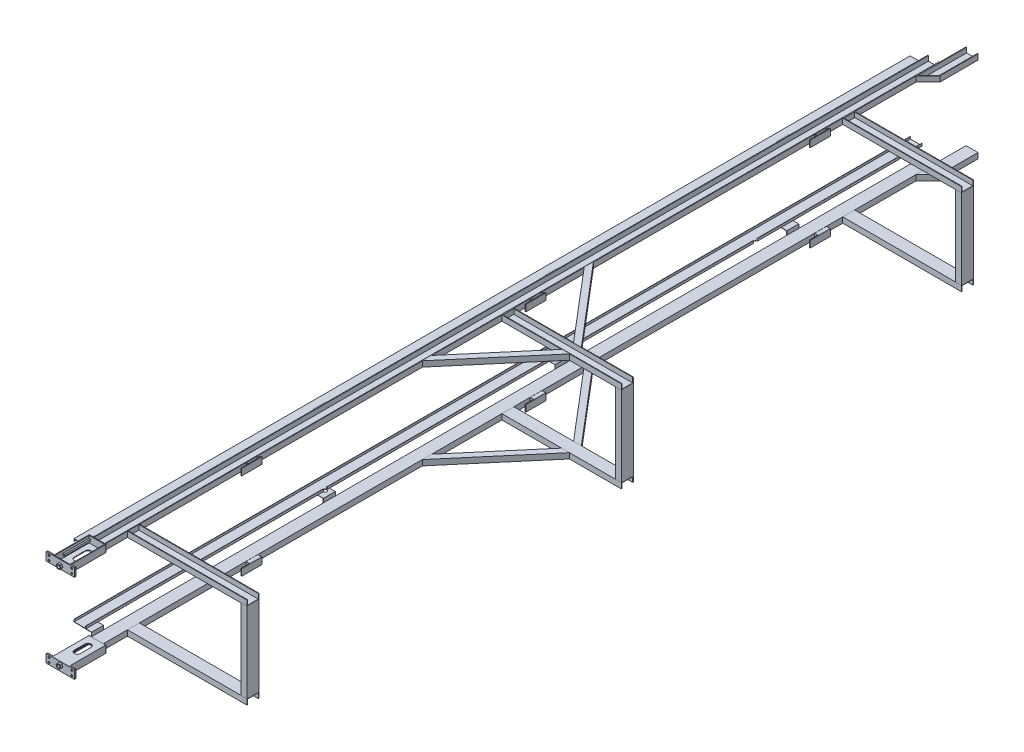
SolidWorks part; units mm, degrees
ref_plane "Front Plane" through (0, 0, 0) normal (0, 0, 1) x (1, 0, 0)
ref_plane "Top Plane" through (0, 0, 0) normal (0, 1, 0) x (1, 0, 0)
ref_plane "Right Plane" through (0, 0, 0) normal (1, 0, 0) x (0, 0, -1)
sketch "Sketch12" plane through (0, 0, 0) normal (0, 0, 1) x (1, 0, 0)
  line L0 (-50, 0) -> (50, 0)
  line L1 (-50, 0) -> (-50, 46)
  line L2 (50, 0) -> (50, 46)
  line L3 (-45, 5) -> (-45, 46)
  line L4 (-45, 5) -> (45, 5)
  line L5 (45, 5) -> (45, 46)
  line L6 (-50, 46) -> (-45, 46)
  line L7 (45, 46) -> (50, 46)
  point P2 (0, 0)
  dimension "D1" = 46
  dimension "D2" = 100
  dimension "D3" = 5
extrude "Boss-Extrude1" add sketch "Sketch12" along normal mid plane 7000
sketch "Sketch24" plane through (0, 46, 0) normal (0, 1, 0) x (1, 0, 0)
  line L0 (50, -3200) -> (1050, -3200)
  line L1 (50, -3500) -> (50, 3500) construction
  line L3 (1050, -3300) -> (50, -3300)
  line L4 (50, -3300) -> (50, -3200)
  line L5 (1050, -3300) -> (1050, -3200)
  line L6 (1050, -3200) -> (1050, 2184.4351) construction
  line L12 (45, -3500) -> (-45, -3500) construction
  line L13 (50, 2855.5299) -> (50, -3200) construction
  line L20 (50, -3200) -> (356.6139, -3200) construction
  line L21 (1050, -3200) -> (1050, -2197.7251) construction
  line L22 (50, -3200) -> (50, 1395.9752) construction
  line L23 (50, -65.672) -> (1050, -65.672)
  line L24 (50, -165.672) -> (1050, -165.672)
  line L25 (1050, -65.672) -> (1050, -165.672)
  line L26 (50, -165.672) -> (50, -65.672)
  line L27 (50, 2687.522) -> (1043.7553, 2687.522)
  line L28 (50, 2787.522) -> (1042.4967, 2787.522) construction
  line L29 (50, 2687.522) -> (50, 2787.522)
  line L30 (50, 2787.522) -> (1043.7553, 2787.522)
  line L31 (1043.7553, 2787.522) -> (1043.7553, 2687.522)
  dimension "D1" = 200
  dimension "D2" = 100
  dimension "D3" = 1000
  dimension "D6" = 100
extrude "Boss-Extrude10" add sketch "Sketch24" against normal blind 46 separate body
shell "Shell1" thickness 5
shell "Shell2" thickness 5
sketch "Sketch31" plane through (0, 46, 0) normal (0, 1, 0) x (1, 0, 0)
  line L0 (50, 2551.1384) -> (77.987, 2551.1384)
  line L1 (77.987, 2551.1384) -> (77.987, 2451.1384)
  line L2 (77.987, 2451.1384) -> (50, 2451.1384)
  line L4 (50, -3500) -> (50, 3500) construction
  line L5 (50, 2451.1384) -> (50, 2551.1384)
  dimension "D1" = 100
  dimension "D2" = 27.987
extrude "Boss-Extrude15" add sketch "Sketch31" against normal blind 45 separate body
shell "Shell4" thickness 5
sketch "Sketch33" plane through (77.987, 0, -5338.5198) normal (-1, 0, 0) x (0, 0, 1)
  line L9 (2787.3813, 1) -> (2957.3813, 1)
  line L10 (2787.3813, 1) -> (2787.3813, 56)
  line L11 (2787.3813, 56) -> (2957.3813, 56)
  line L12 (2957.3813, 1) -> (2957.3813, 56)
  dimension "D1" = 170
  dimension "D2" = 55
extrude "Boss-Extrude23" add sketch "Sketch33" against normal blind 6 separate body
pattern_linear "LPattern2" count 3 spacing 2380 along (0, 0, 1) of bodies 132 145
sketch "Sketch34" plane through (0, 0, 3500) normal (0, 0, 1) x (1, 0, 0)
  line L0 (-70, 0) -> (70, 0)
  line L1 (-50, 0) -> (50, 0) construction
  line L2 (-70, 0) -> (-70, 60)
  line L3 (0, 0) -> (0, 71.8206) construction
  line L4 (70, 0) -> (70, 60)
  line L10 (70, 60) -> (-70, 60)
  point P4 (0, 0)
  point P5 (0, 0)
  dimension "D1" = 140
  dimension "D2" = 60
extrude "Boss-Extrude25" add sketch "Sketch34" along normal blind 6 separate body
sketch "Sketch35" plane through (0, 0, 3506) normal (0, 0, 1) x (1, 0, 0)
  line L0 (70, 0) -> (70, 60) construction
  line L1 (-70, 0) -> (70, 0) construction
  line L2 (-70, 60) -> (-70, 0) construction
  line L3 (70, 0) -> (70, 60)
  line L4 (-70, 0) -> (70, 0)
  line L5 (-70, 60) -> (-70, 0)
  line L6 (-65, 60) -> (-65, 5)
  line L7 (-65, 5) -> (65, 5)
  line L8 (65, 5) -> (65, 60)
  line L9 (-70, 60) -> (-65, 60)
  line L10 (70, 60) -> (65, 60)
  dimension "D1" = 5
extrude "Boss-Extrude26" add sketch "Sketch35" along normal blind 300 separate body
sketch "Sketch36" plane through (0, 0, 3506) normal (0, 0, 1) x (1, 0, 0)
  line L0 (0, 0) -> (0, 40.4824) construction
  line L1 (-65, 5) -> (-65, 60) construction
  line L2 (-65, 39) -> (-52, 39)
  line L3 (-65, 39) -> (-65, 23)
  line L4 (-65, 23) -> (-52, 23)
  line L5 (-52, 39) -> (-52, 23)
  line L6 (52, 39) -> (52, 23)
  line L7 (65, 23) -> (52, 23)
  line L8 (65, 39) -> (65, 23)
  line L9 (65, 39) -> (52, 39)
  line L10 (65, 5) -> (-65, 5) construction
  dimension "D1" = 18
  dimension "D2" = 16
  dimension "D3" = 13
extrude "Boss-Extrude27" add sketch "Sketch36" along normal blind 220 separate body
sketch "Sketch37" plane through (0, 0, 3806) normal (0, 0, 1) x (1, 0, 0)
  line L0 (120, 0) -> (-120, 0)
  line L4 (0, 70) -> (0, 0) construction
  line L8 (-120, 70) -> (-120, 0)
  line L9 (120, 70) -> (120, 0)
  line L12 (-95.1007, 70) -> (-95.1007, 0) construction
  line L13 (-95.1007, 35) -> (-108.4029, 35) construction
  line L14 (-120, 70) -> (120, 70)
  circle A0 centre (-95.1007, 53.4578) radius 8
  circle A1 centre (-95.1007, 16.5422) radius 8
  circle A2 centre (95.1007, 16.5422) radius 8
  circle A3 centre (95.1007, 53.4578) radius 8
  point P7 (-120, 35)
  dimension "D4" = 16
  dimension "D1" = 240
  dimension "D2" = 70
extrude "Boss-Extrude28" add sketch "Sketch37" along normal blind 6 separate body
sketch "Sketch39" plane through (0, 0, 3806) normal (0, 0, -1) x (-1, 0, 0)
  line L0 (0, 0) -> (0, 26)
  circle A0 centre (0, 26) radius 13
  dimension "D2" = 26
  dimension "D1" = 26
extrude "Cut-Extrude3" cut sketch "Sketch39" against normal blind 6
sketch "Sketch43" plane through (0, 46, 0) normal (0, 1, 0) x (1, 0, 0)
  line L0 (50, 3400.0313) -> (50, 3720.0313)
  line L1 (50, -3500) -> (50, 3500) construction
  line L2 (50, 3720.0313) -> (150, 3720.0313)
  line L3 (150, 3720.0313) -> (150, 3400.0313)
  line L6 (50, 3500) -> (150, 3500) construction
  line L7 (50, 3400.0313) -> (150, 3400.0313) construction
  line L8 (150, 3400.0313) -> (50, 3300.0313)
  line L9 (50, 3400.0313) -> (50, 3300.0313)
  line L10 (45, 3500) -> (-45, 3500) construction
  dimension "D1" = 100
  dimension "D2" = 420
  dimension "D3" = 199.9687
  dimension "D4" = 100
extrude "Boss-Extrude31" add sketch "Sketch43" against normal blind 46 separate body
shell "Shell6" thickness 5
ref_plane "Plane1" through (0, -335, 0) normal (0, -1, 0) x (-1, 0, 0)
sketch "Sketch41" plane through (0, 5, 0) normal (0, 1, 0) x (1, 0, 0)
  line L0 (0, -3506) -> (0, -3249.3372) construction
  line L1 (65, -3506) -> (-65, -3506) construction
  line L2 (0, -3580) -> (0, -3670) construction
  line L3 (25, -3580) -> (25, -3670)
  line L4 (-25, -3580) -> (-25, -3670)
  line L5 (70, -3500) -> (-70, -3500) construction
  arc A0 (25, -3580) -> (-25, -3580) centre (0, -3580) ccw
  arc A1 (-25, -3670) -> (25, -3670) centre (0, -3670) ccw
  point P7 (0, -3625)
  point P13 (0, -3555)
  point P14 (0, -3695)
  dimension "D1" = 50
  dimension "D2" = 140
  dimension "D3" = 55
extrude "Cut-Extrude4" cut sketch "Sketch41" against normal blind 16
sketch "Sketch57" plane through (-70, 0, 0) normal (-1, 0, 0) x (0, 0, 1)
  line L0 (3806, 0) -> (3506, 0) construction
  line L1 (3806, 70) -> (3800, 70)
  line L2 (3806, 70) -> (3806, 0)
  line L3 (3806, 0) -> (3800, 0)
  line L4 (3800, 70) -> (3800, 0)
  dimension "D1" = 6
extrude "Boss-Extrude44" add sketch "Sketch57" along normal up to vertex (50 mm away) separate body
sketch "Sketch58" plane through (0, 0, 3806) normal (0, 0, 1) x (1, 0, 0)
  circle A0 centre (-95.1007, 53.4578) radius 8 construction
  circle A1 centre (-95.1007, 16.5422) radius 8 construction
  circle A2 centre (-95.1007, 53.4578) radius 8
  circle A3 centre (-95.1007, 16.5422) radius 8
extrude "Cut-Extrude6" cut sketch "Sketch58" against normal blind 50
shell "Shell7" thickness 5
sketch "Sketch59" plane through (0, 0, 3806) normal (0, 0, -1) x (-1, 0, 0)
  line L1 (-120, 70) -> (-70, 70)
  line L2 (-120, 70) -> (-120, 0)
  line L3 (-120, 0) -> (-70, 0)
  line L4 (-70, 70) -> (-70, 0)
  circle A0 centre (-95.1007, 16.5422) radius 8 construction
  circle A1 centre (-95.1007, 53.4578) radius 8 construction
  circle A2 centre (-95.1007, 16.5422) radius 8
  circle A3 centre (-95.1007, 53.4578) radius 8
extrude "Boss-Extrude45" add sketch "Sketch59" along normal blind 6 separate body
fillet "Fillet1" radius 5 4 edges at (-120, 0, 3809) (-120, 70, 3809) (120, 70, 3809) (120, 0, 3809)
fillet "Fillet2" radius 5 2 edges at (120, 70, 3803) (120, 0, 3803)
fillet "Fillet3" radius 5 2 edges at (-120, 70, 3803) (-120, 0, 3803)
sketch "Sketch60" plane through (0, 46, 0) normal (0, 1, 0) x (1, 0, 0)
  line L0 (50, 523.1112) -> (550, -65.672)
  line L1 (50, -3500) -> (50, 3500) construction
  line L2 (1050, -65.672) -> (50, -65.672) construction
  line L3 (550, -65.672) -> (615.5964, -65.672)
  line L4 (615.5964, -65.672) -> (50, 600.3553)
  line L5 (50, 600.3553) -> (50, 523.1112)
  line L6 (1050, -115.672) -> (423.7069, -115.672) construction
  line L7 (1050, -160.672) -> (1050, -70.672) construction
  line L8 (50, -831.6993) -> (50, -754.4552)
  line L9 (615.5964, -165.672) -> (50, -831.6993)
  line L10 (550, -165.672) -> (615.5964, -165.672)
  line L11 (50, -754.4552) -> (550, -165.672)
  dimension "D1" = 50
extrude "Boss-Extrude46" add sketch "Sketch60" against normal up to surface (46 mm away) separate body up to face at (550, 0, 115.672)
mirror "Mirror1" about plane through (0, -335, 0) normal (0, -1, 0) of bodies 156 205 214 158 153 154 151 102 121 149 147 211 148 146 132 145 212 175 216 215 213
sketch "Sketch61" plane through (0, 0, 3812) normal (0, 0, 1) x (1, 0, 0)
  line L1 (12.158, 43.2116) -> (-8.8267, 45.135)
  line L2 (-8.8267, 45.135) -> (-20.9847, 27.9234)
  line L3 (-20.9847, 27.9234) -> (-12.158, 8.7884)
  line L4 (-12.158, 8.7884) -> (8.8267, 6.865)
  line L5 (8.8267, 6.865) -> (20.9847, 24.0766)
  line L6 (20.9847, 24.0766) -> (12.158, 43.2116)
  line L7 (-20.5282, -691.2406) -> (-14.3859, -711.3982)
  line L8 (-14.3859, -711.3982) -> (6.1423, -716.1576)
  line L9 (6.1423, -716.1576) -> (20.5282, -700.7594)
  line L10 (20.5282, -700.7594) -> (14.3859, -680.6018)
  line L11 (14.3859, -680.6018) -> (-6.1423, -675.8424)
  line L12 (-6.1423, -675.8424) -> (-20.5282, -691.2406)
  circle A0 centre (0, 26) radius 18.2495 construction
  circle A1 centre (0, 26) radius 13
  circle A2 centre (0, -696) radius 13 construction
  circle A3 centre (0, -696) radius 13
  circle A4 centre (0, -696) radius 18.2495 construction
extrude "Boss-Extrude47" add sketch "Sketch61" along normal blind 15 separate body
sketch "Sketch63" plane through (0, 0, 0) normal (0, -1, 0) x (1, 0, 0)
  line L0 (50, -2687.522) -> (1043.7553, -2687.522) construction
  line L1 (1043.7553, -2787.522) -> (993.7553, -2787.522)
  line L2 (1043.7553, -2787.522) -> (1043.7553, -2687.522)
  line L3 (1043.7553, -2687.522) -> (993.7553, -2687.522)
  line L4 (993.7553, -2787.522) -> (993.7553, -2687.522)
  line L5 (50, 165.672) -> (1050, 165.672) construction
  line L6 (1050, 65.672) -> (1000, 65.672)
  line L7 (1050, 65.672) -> (1050, 165.672)
  line L8 (1050, 165.672) -> (1000, 165.672)
  line L9 (1000, 65.672) -> (1000, 165.672)
  line L10 (50, 3300) -> (1050, 3300) construction
  line L11 (1050, 3200) -> (1000, 3200)
  line L12 (1050, 3200) -> (1050, 3300)
  line L13 (1050, 3300) -> (1000, 3300)
  line L14 (1000, 3200) -> (1000, 3300)
  dimension "D1" = 50
extrude "Boss-Extrude48" add sketch "Sketch63" along normal up to surface (670 mm away) separate body up to face at (550, -670, 115.672)
sketch "Sketch64" plane through (0, 0, 0) normal (0, 0, 1) x (1, 0, 0)
  line L0 (993.7553, -335) -> (-100, -335) construction
  line L1 (993.7553, -670) -> (993.7553, 0) construction
  line L2 (-100, -335) -> (-100, -35) construction
  line L3 (-100, -53) -> (-100, -35)
  line L4 (-100, -35) -> (-196, -35)
  line L5 (-196, -35) -> (-196, -53)
  line L6 (-98, -53) -> (-98, -33)
  line L7 (-98, -33) -> (-198, -33)
  line L8 (-198, -33) -> (-198, -53)
  line L9 (-98, -53) -> (-100, -53)
  line L10 (-196, -53) -> (-198, -53)
  line L11 (-70, 0) -> (-70, 70) construction
  dimension "D1" = 300
  dimension "D3" = 100
  dimension "D4" = 30
  dimension "D5" = 20
  dimension "D2" = 2
extrude "Boss-Extrude49" add sketch "Sketch64" along normal mid plane 7000 separate body
sketch "Sketch65" plane through (0, 0, 3500) normal (0, 0, 1) x (1, 0, 0)
  line L0 (-50, 29.4046) -> (-50, 0)
  line L1 (-50, 0) -> (-50, -33)
  line L2 (-50, -33) -> (-135.1481, -33)
  line L3 (-98, -33) -> (-198, -33) construction
  line L4 (-52, 29.4046) -> (-52, 0)
  line L5 (-52, 0) -> (-52, -31)
  line L6 (-52, -31) -> (-135.1481, -31)
  line L7 (-50, 29.4046) -> (-52, 29.4046)
  line L8 (-135.1481, -31) -> (-135.1481, -33)
  dimension "D1" = 2
extrude "Boss-Extrude50" add sketch "Sketch65" against normal blind 100 separate body
pattern_linear "LPattern3" count 4 spacing 1940 along (0, 0, -1) of bodies 245
mirror "Mirror2" about plane through (0, -335, 0) normal (0, -1, 0) of bodies 248 244 247 245 246
sketch "Sketch66" plane through (0, -33, 0) normal (0, 1, 0) x (1, 0, 0)
  line L0 (-148, -3500) -> (-148, -1496.97) construction
  line L1 (-98, -3500) -> (-198, -3500) construction
  line L2 (-148, -1496.97) -> (-98, -1496.97) construction
  line L3 (-98, -3500) -> (-98, 3500) construction
  line L4 (-98, 3500) -> (-98, 2103.03) construction
  line L5 (-98, 3500) -> (-198, 3500) construction
  circle A0 centre (-98, -1496.97) radius 15
  circle A1 centre (-98, 2103.03) radius 15
  dimension "D1" = 30
  dimension "D3" = 30
  dimension "D4" = 1396.97
  dimension "D2" = 2003.03
extrude "Cut-Extrude8" cut sketch "Sketch66" against normal blind 1459
